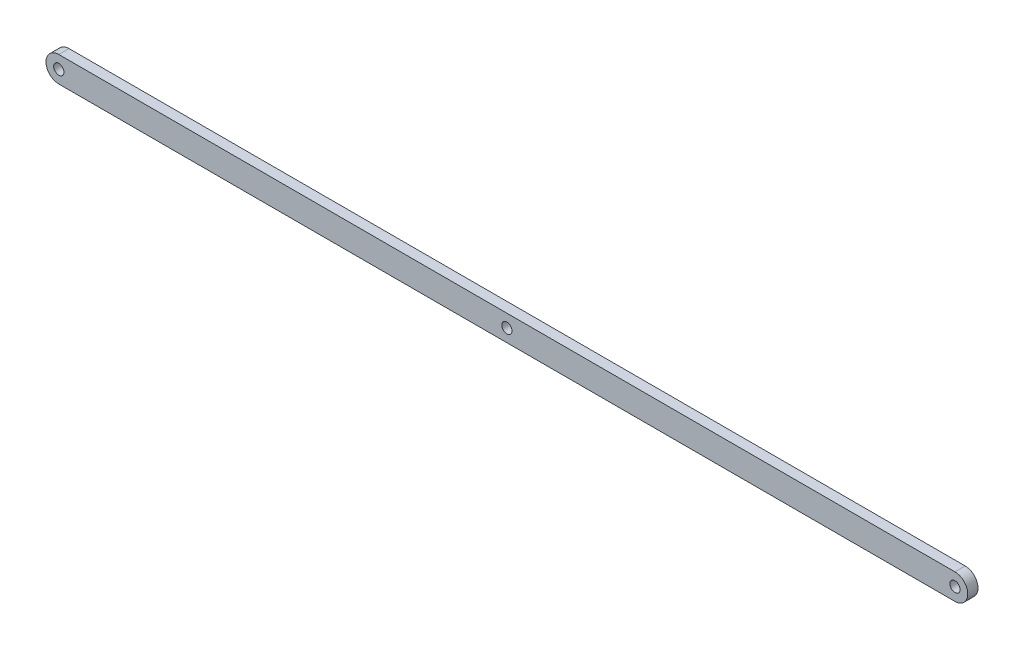
SolidWorks part; units mm, degrees
ref_plane "Front Plane" through (0, 0, 0) normal (0, 0, 1) x (1, 0, 0)
ref_plane "Top Plane" through (0, 0, 0) normal (0, 1, 0) x (1, 0, 0)
ref_plane "Right Plane" through (0, 0, 0) normal (1, 0, 0) x (0, 0, -1)
sketch "Sketch1" plane through (0, 0, 0) normal (0, 0, 1) x (1, 0, 0)
  line L1 (-111.125, 3.175) -> (111.125, 3.175)
  line L2 (-111.125, 3.175) -> (-111.125, -3.175)
  line L3 (-111.125, -3.175) -> (111.125, -3.175)
  line L4 (111.125, 3.175) -> (111.125, -3.175)
  line L5 (-111.125, 3.175) -> (111.125, -3.175) construction
  line L6 (-111.125, -3.175) -> (111.125, 3.175) construction
  circle A0 centre (-111.125, 0) radius 3.175
  circle A1 centre (111.125, 0) radius 3.175
  circle A2 centre (-111.125, 0) radius 1.27
  circle A3 centre (111.125, 0) radius 1.27
  circle A4 centre (0, 0) radius 1.27
  point P0 (0, 0)
  point P11 (-111.125, 0)
  point P13 (111.125, 0)
  point P16 (0, 0)
  dimension "D3" = 6.35
  dimension "D4" = 6.35
  dimension "D5" = 2.54
  dimension "D6" = 2.54
  dimension "D7" = 2.54
  dimension "D1" = 6.35
  dimension "D2" = 222.25
extrude "Boss-Extrude1" add sketch "Sketch1" along normal blind 2.54 contours A1 L1 A0 L3 | A2 L2 A0 | A2 L2 A0 | A3 L4 A1 | A3 L4 A1
